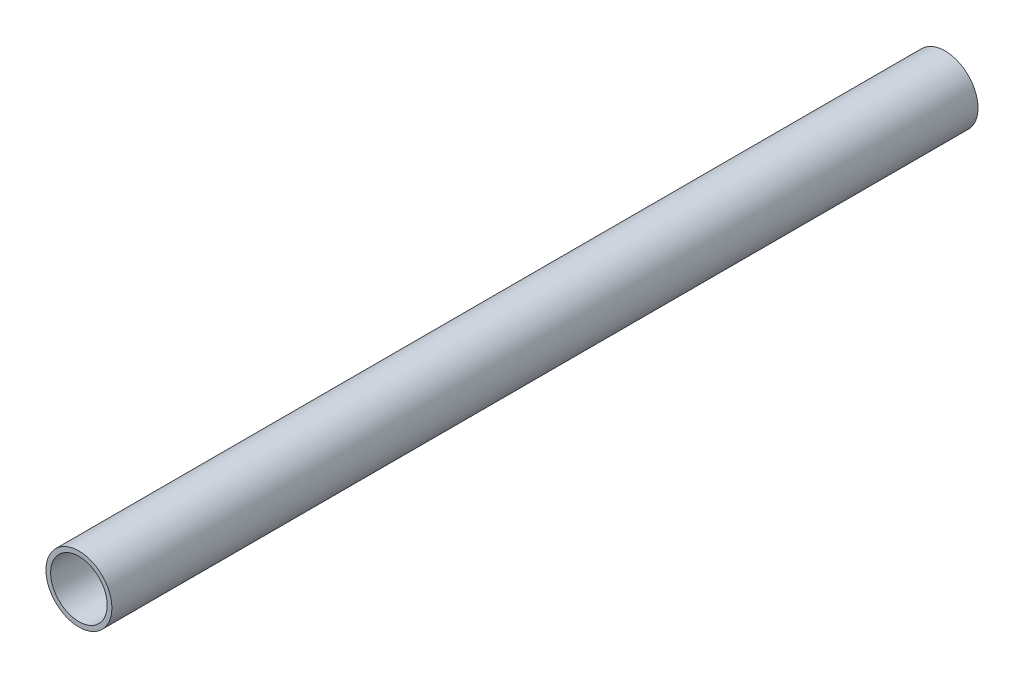
SolidWorks part; units mm, degrees
material "PVC Rigid"
ref_plane "Front Plane" through (0, 0, 0) normal (0, 0, 1) x (1, 0, 0)
ref_plane "Top Plane" through (0, 0, 0) normal (0, 1, 0) x (1, 0, 0)
ref_plane "Right Plane" through (0, 0, 0) normal (1, 0, 0) x (0, 0, -1)
sketch "Sketch1" plane through (0, 0, 0) normal (0, 0, 1) x (1, 0, 0)
  circle A1 centre (0, 0) radius 12.573
  circle A2 centre (0, 0) radius 10.795
  dimension "D1" = 25.146
  dimension "D2" = 21.59
extrude "Boss-Extrude1" add sketch "Sketch1" along normal blind 330.2
